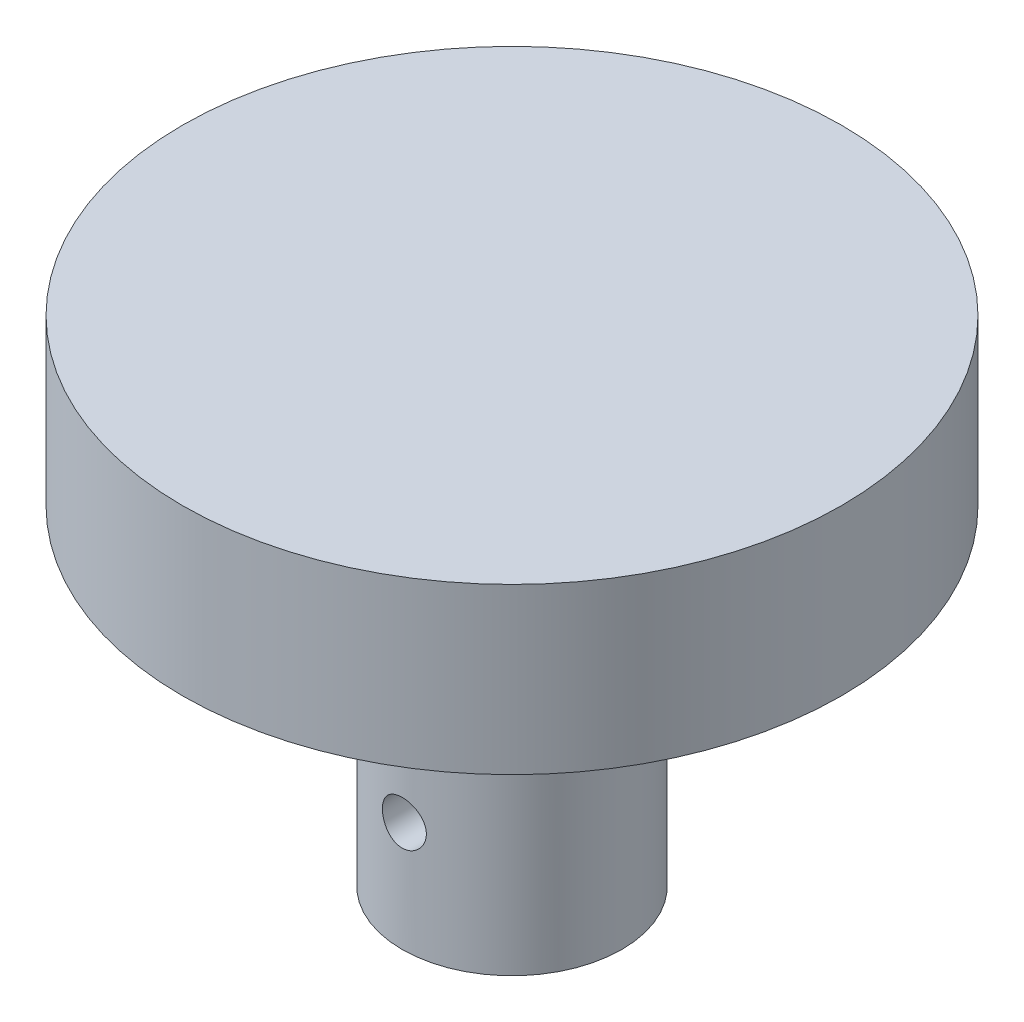
SolidWorks part; units mm, degrees
ref_plane "Front Plane" through (0, 0, 0) normal (0, 0, 1) x (1, 0, 0)
ref_plane "Top Plane" through (0, 0, 0) normal (0, 1, 0) x (1, 0, 0)
ref_plane "Right Plane" through (0, 0, 0) normal (1, 0, 0) x (0, 0, -1)
sketch "Sketch1" plane through (0, 0, 0) normal (0, 1, 0) x (1, 0, 0)
  circle A0 centre (0, 0) radius 19.05
  circle A1 centre (0, 0) radius 3.5 construction
  dimension "D1" = 38.1
  dimension "D2" = 7
extrude "Boss-Extrude1" add sketch "Sketch1" along normal blind 9.525
sketch "Sketch2" plane through (0, 0, 0) normal (0, -1, 0) x (1, 0, 0)
  circle A0 centre (0, 0) radius 3.5
  circle A1 centre (0, 0) radius 6.35
  dimension "D1" = 12.7
  dimension "D2" = 7
extrude "Boss-Extrude2" add sketch "Sketch2" along normal blind 19.05
ref_plane "Plane1" through (0, 0, 6.35) normal (0, 0, 1) x (1, 0, 0)
sketch "Sketch3" plane through (0, 0, 6.35) normal (0, 0, 1) x (1, 0, 0)
  line L0 (-6.35, -19.05) -> (6.35, -19.05) construction
  circle A0 centre (0, -12.7) radius 1.27
  dimension "D1" = 2.54
  dimension "D2" = 6.35
extrude "Cut-Extrude1" cut sketch "Sketch3" against normal up to surface (3.0885 mm away)
